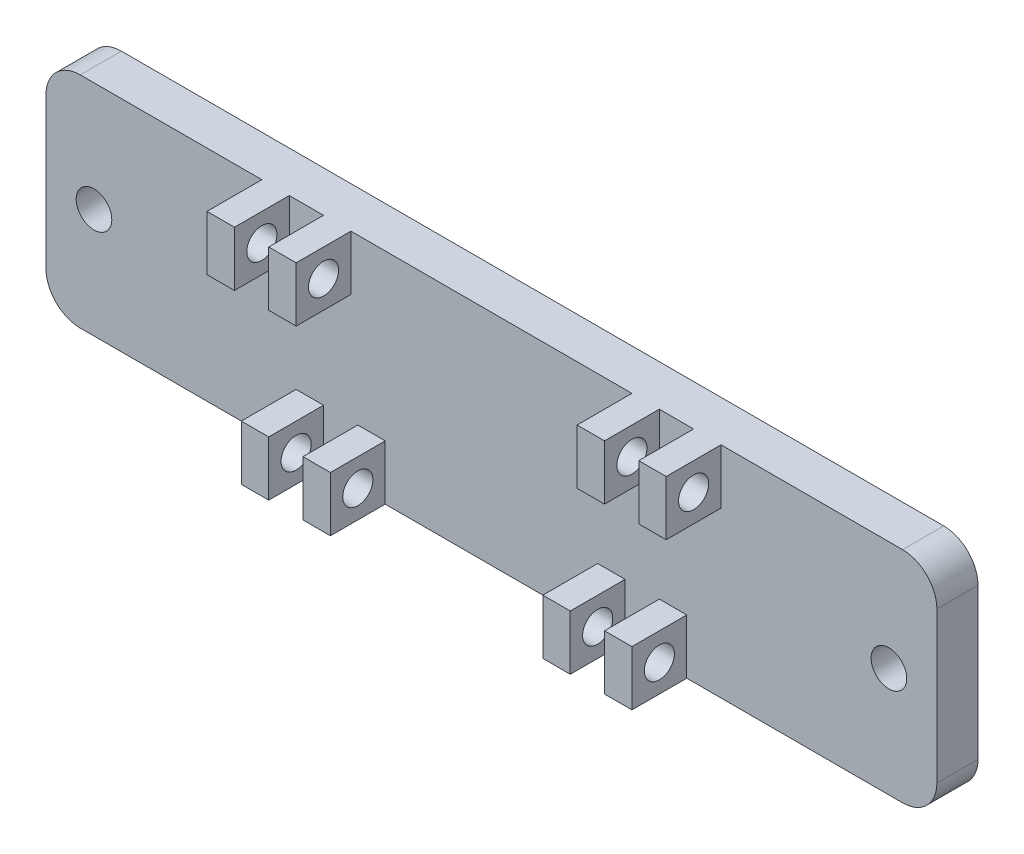
SolidWorks part; units mm, degrees
ref_plane "前视基准面" through (0, 0, 0) normal (0, 0, 1) x (1, 0, 0)
ref_plane "上视基准面" through (0, 0, 0) normal (0, 1, 0) x (1, 0, 0)
ref_plane "右视基准面" through (0, 0, 0) normal (1, 0, 0) x (0, 0, -1)
sketch "草图2" plane through (0, 0, 0) normal (0, 0, 1) x (1, 0, 0)
  line L0 (61.5, -4.5) -> (-3.5, -4.5) construction
  line L1 (-1, -12.5) -> (59, -12.5)
  line L2 (-3.5, -10) -> (-3.5, 1)
  line L4 (61.5, 1) -> (61.5, -10)
  line L5 (29, 3.5) -> (29, -12.5) construction
  line L10 (59, 3.5) -> (-1, 3.5)
  arc A2 (-1, 3.5) -> (-3.5, 1) centre (-1, 1) ccw
  arc A3 (61.5, 1) -> (59, 3.5) centre (59, 1) ccw
  circle A6 centre (0, -4.5) radius 1.3
  circle A7 centre (58, -4.5) radius 1.3
  arc A12 (59, -12.5) -> (61.5, -10) centre (59, -10) ccw
  arc A13 (-3.5, -10) -> (-1, -12.5) centre (-1, -10) ccw
  point P8 (0, 0)
  point P9 (0, 0)
  point P31 (-3.5, -12.5)
  dimension "D4" = 3.5
  dimension "D5" = 3.5
  dimension "D6" = 2.5
  dimension "D7" = 2.5
  dimension "D8" = 2.5
  dimension "D9" = 2.5
  dimension "D1" = 65
  dimension "D2" = 2.6
  dimension "D3" = 58
extrude "凸台-拉伸2" add sketch "草图2" along normal blind 3 contours L2 A13 L1 A12 L4 A3 L10 A2 A7 A6
sketch "草图4" plane through (0, 0, 3) normal (0, 0, 1) x (1, 0, 0)
  line L0 (29, 3.5) -> (29, -12.5) construction
  line L1 (12.25, 1.5) -> (18.75, 1.5) construction
  line L4 (59, 3.5) -> (-1, 3.5)
  line L5 (-1, -12.5) -> (59, -12.5)
  line L7 (61.5, -10) -> (61.5, 1)
  line L14 (12.25, 3.5) -> (18.75, 3.5)
  line L15 (12.25, 3.5) -> (12.25, -0.5)
  line L16 (12.25, -0.5) -> (18.75, -0.5)
  line L17 (18.75, 3.5) -> (18.75, -0.5)
  line L18 (43.75, -0.5) -> (41.25, 3.5) construction
  line L19 (14.25, 3.5) -> (16.75, 3.5)
  line L20 (14.25, 3.5) -> (14.25, -0.5)
  line L21 (14.25, -0.5) -> (16.75, -0.5)
  line L22 (16.75, 3.5) -> (16.75, -0.5)
  line L23 (14.25, 3.5) -> (16.75, -0.5) construction
  line L24 (14.25, -0.5) -> (16.75, 3.5) construction
  line L25 (43.75, 3.5) -> (41.25, -0.5) construction
  line L26 (45.75, 1.5) -> (39.25, 1.5) construction
  line L27 (41.25, 3.5) -> (41.25, -0.5)
  line L28 (43.75, -0.5) -> (41.25, -0.5)
  line L29 (43.75, 3.5) -> (43.75, -0.5)
  line L30 (43.75, 3.5) -> (41.25, 3.5)
  line L31 (39.25, 3.5) -> (39.25, -0.5)
  line L32 (45.75, -0.5) -> (39.25, -0.5)
  line L33 (45.75, 3.5) -> (45.75, -0.5)
  line L34 (45.75, 3.5) -> (39.25, 3.5)
  line L35 (14.75, -10.5) -> (21.25, -10.5) construction
  line L36 (14.75, -12.5) -> (21.25, -12.5)
  line L37 (14.75, -12.5) -> (14.75, -8.5)
  line L38 (14.75, -8.5) -> (21.25, -8.5)
  line L39 (21.25, -12.5) -> (21.25, -8.5)
  line L40 (41.25, -8.5) -> (38.75, -12.5) construction
  line L41 (16.75, -12.5) -> (19.25, -12.5)
  line L42 (16.75, -12.5) -> (16.75, -8.5)
  line L43 (16.75, -8.5) -> (19.25, -8.5)
  line L44 (19.25, -12.5) -> (19.25, -8.5)
  line L45 (16.75, -12.5) -> (19.25, -8.5) construction
  line L46 (16.75, -8.5) -> (19.25, -12.5) construction
  line L47 (41.25, -12.5) -> (38.75, -8.5) construction
  line L48 (43.25, -10.5) -> (36.75, -10.5) construction
  line L49 (38.75, -12.5) -> (38.75, -8.5)
  line L50 (41.25, -8.5) -> (38.75, -8.5)
  line L51 (41.25, -12.5) -> (41.25, -8.5)
  line L52 (41.25, -12.5) -> (38.75, -12.5)
  line L53 (36.75, -12.5) -> (36.75, -8.5)
  line L54 (43.25, -8.5) -> (36.75, -8.5)
  line L55 (43.25, -12.5) -> (43.25, -8.5)
  line L56 (43.25, -12.5) -> (36.75, -12.5)
  line L62 (-1, -12.5) -> (59, -12.5)
  line L64 (-3.5, 1) -> (-3.5, -10)
  line L65 (-3.5, 1) -> (-3.5, -10)
  line L66 (59, 3.5) -> (-1, 3.5)
  line L67 (61.5, -10) -> (61.5, 1)
  arc A6 (61.5, 1) -> (59, 3.5) centre (59, 1) ccw
  arc A7 (61.5, 1) -> (59, 3.5) centre (59, 1) ccw
  arc A8 (-3.5, -10) -> (-1, -12.5) centre (-1, -10) ccw
  arc A10 (-3.5, -10) -> (-1, -12.5) centre (-1, -10) ccw
  arc A12 (59, -12.5) -> (61.5, -10) centre (59, -10) ccw
  arc A13 (59, -12.5) -> (61.5, -10) centre (59, -10) ccw
  arc A14 (-1, 3.5) -> (-3.5, 1) centre (-1, 1) ccw
  arc A15 (-1, 3.5) -> (-3.5, 1) centre (-1, 1) ccw
  point P4 (0, 0)
  point P5 (0, 0)
  point P16 (15.5, 1.5)
  point P31 (42.5, 1.5)
  point P38 (18, -10.5)
  point P53 (40, -10.5)
  dimension "D2" = 4
  dimension "D3" = 6.5
  dimension "D4" = 2.5
  dimension "D5" = 27
  dimension "D6" = 2.5
  dimension "D7" = 6.5
  dimension "D8" = 0
  dimension "D1" = 0
extrude "凸台-拉伸3" add sketch "草图4" along normal blind 4
sketch "草图6" plane through (12.25, 0, 0) normal (-1, 0, 0) x (0, 0, 1)
  line L0 (7, 3.5) -> (3, -0.5) construction
  line L1 (7, -8.5) -> (3, -12.5) construction
  line L4 (3, 3.5) -> (3, -0.5)
  line L5 (3, -0.5) -> (7, -0.5)
  line L6 (7, -0.5) -> (7, 3.5)
  line L9 (3, -0.5) -> (7, -0.5)
  line L10 (7, -0.5) -> (7, 3.5)
  line L12 (3, -8.5) -> (3, -12.5)
  line L13 (3, -12.5) -> (7, -12.5)
  line L14 (7, -12.5) -> (7, -8.5)
  line L15 (7, -8.5) -> (3, -8.5)
  line L16 (3, -8.5) -> (3, -12.5)
  line L17 (3, -12.5) -> (7, -12.5)
  line L18 (7, -12.5) -> (7, -8.5)
  line L19 (7, -8.5) -> (3, -8.5)
  line L22 (7, 3.5) -> (3, 3.5)
  line L23 (7, 3.5) -> (3, 3.5)
  line L24 (3, 3.5) -> (3, -0.5)
  circle A0 centre (5, 1.5) radius 1.1
  circle A1 centre (5, -10.5) radius 1.1
  dimension "D3" = 2.2
  dimension "D4" = 2.2
  dimension "D1" = 0
  dimension "D2" = 0
extrude "切除-拉伸2" cut sketch "草图6" against normal through all contours A0 | A1
